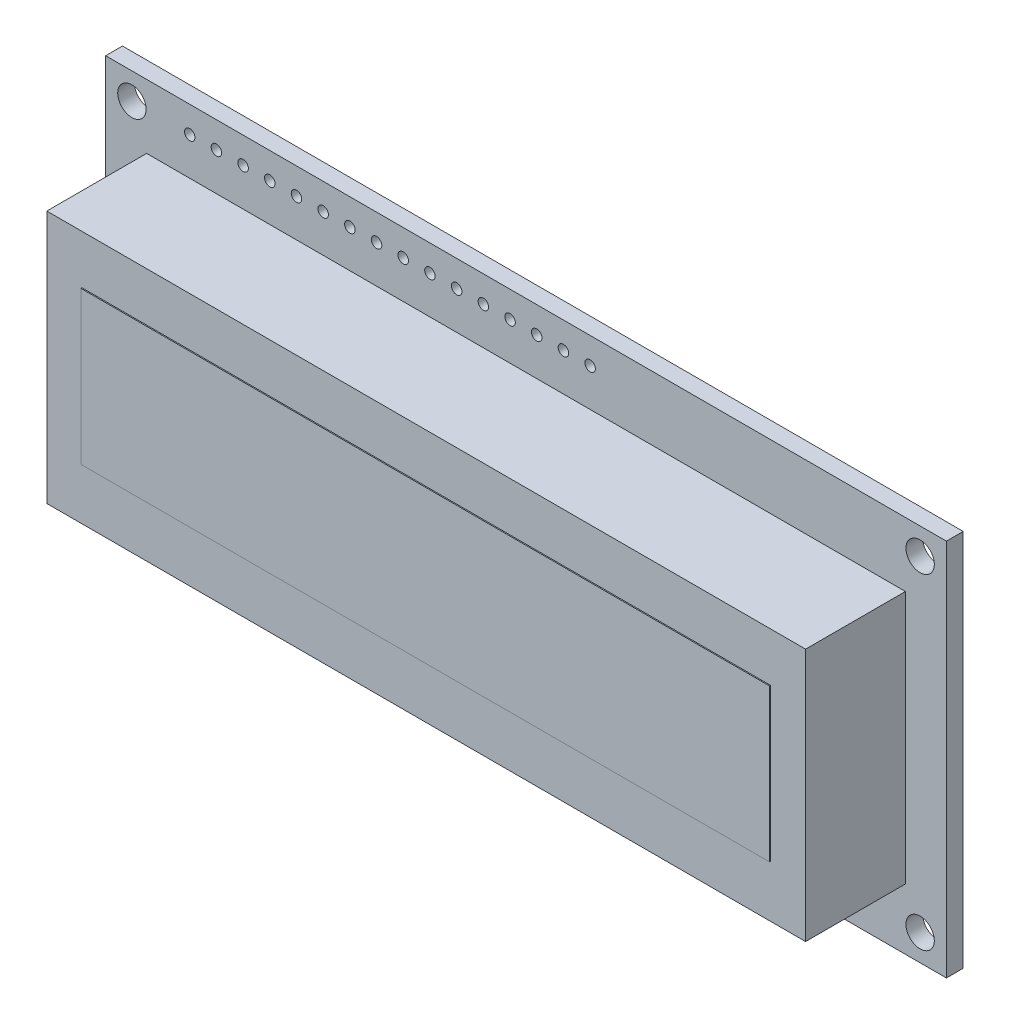
SolidWorks part; units mm, degrees
ref_plane "Plano frontal" through (0, 0, 0) normal (0, 0, 1) x (1, 0, 0)
ref_plane "Plano superior" through (0, 0, 0) normal (0, 1, 0) x (1, 0, 0)
ref_plane "Plano direito" through (0, 0, 0) normal (1, 0, 0) x (0, 0, -1)
sketch "Esboço1" plane through (0, 0, 0) normal (0, 0, 1) x (1, 0, 0)
  line L0 (2.5, 33.5) -> (77.5, 2.5) construction
  line L1 (0, 0) -> (80, 0)
  line L2 (0, 0) -> (0, 36)
  line L3 (0, 36) -> (80, 36)
  line L4 (80, 0) -> (80, 36)
  line L5 (40, 0) -> (40, 36) construction
  circle A0 centre (2.5, 33.5) radius 1.35
  circle A1 centre (2.5, 2.5) radius 1.35
  circle A2 centre (77.5, 33.5) radius 1.35
  circle A3 centre (77.5, 2.5) radius 1.35
  point P15 (40, 18)
  dimension "D5" = 2.7
  dimension "D1" = 36
  dimension "D2" = 80
  dimension "D3" = 75
  dimension "D4" = 31
extrude "Ressalto-extrusão1" add sketch "Esboço1" along normal blind 1.6
sketch "Esboço3" plane through (0, 0, 1.6) normal (0, 0, 1) x (1, 0, 0)
  line L0 (0, 0) -> (80, 0) construction
  line L1 (3.9, 29.9) -> (76.1, 29.9)
  line L2 (3.9, 29.9) -> (3.9, 5.8)
  line L3 (3.9, 5.8) -> (76.1, 5.8)
  line L4 (76.1, 29.9) -> (76.1, 5.8)
  line L5 (80, 36) -> (0, 36) construction
  line L6 (40, 29.9) -> (40, 5.8) construction
  line L7 (0, 18) -> (80, 18) construction
  line L8 (0, 36) -> (0, 0) construction
  line L9 (80, 0) -> (80, 36) construction
  point P16 (40, 18)
  dimension "D1" = 5.8
  dimension "D2" = 6.1
  dimension "D3" = 72.2
sketch "Esboço4" plane through (0, 0, 1.6) normal (0, 0, 1) x (1, 0, 0)
  line L0 (7.25, 25.25) -> (72.75, 10.75) construction
  line L1 (7.25, 25.25) -> (72.75, 25.25)
  line L2 (7.25, 25.25) -> (7.25, 10.75)
  line L3 (7.25, 10.75) -> (72.75, 10.75)
  line L4 (72.75, 25.25) -> (72.75, 10.75)
  dimension "D1" = 14.5
  dimension "D2" = 65.5
extrude "Ressalto-extrusão2" add sketch "Esboço4" along normal blind 9.6
extrude "Ressalto-extrusão3" add sketch "Esboço3" along normal blind 9.5 contours L1 L4 L3 L2
sketch "Esboço5" plane through (0, 0, 1.6) normal (0, 0, 1) x (1, 0, 0)
  line L0 (0, 36) -> (0, 0) construction
  line L1 (80, 36) -> (0, 36) construction
  circle A0 centre (8, 33.5) radius 0.5
  circle A1 centre (10.54, 33.5) radius 0.5
  circle A2 centre (13.08, 33.5) radius 0.5
  circle A3 centre (15.62, 33.5) radius 0.5
  circle A4 centre (18.16, 33.5) radius 0.5
  circle A5 centre (20.7, 33.5) radius 0.5
  circle A6 centre (23.24, 33.5) radius 0.5
  circle A7 centre (25.78, 33.5) radius 0.5
  circle A8 centre (28.32, 33.5) radius 0.5
  circle A9 centre (30.86, 33.5) radius 0.5
  circle A10 centre (33.4, 33.5) radius 0.5
  circle A11 centre (35.94, 33.5) radius 0.5
  circle A12 centre (38.48, 33.5) radius 0.5
  circle A13 centre (41.02, 33.5) radius 0.5
  circle A14 centre (43.56, 33.5) radius 0.5
  circle A15 centre (46.1, 33.5) radius 0.5
  dimension "D3" = 1
  dimension "D1" = 8
  dimension "D2" = 2.5
  dimension "D4" = 16
extrude "Corte-extrusão1" cut sketch "Esboço5" against normal through all
